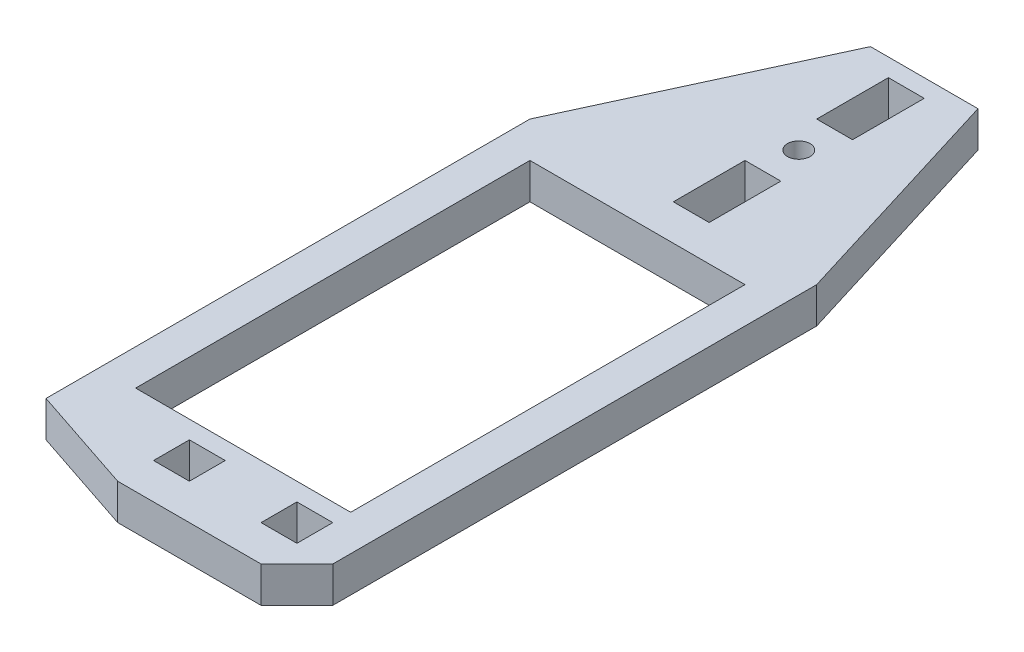
SolidWorks part; units mm, degrees
ref_plane "Front Plane" through (0, 0, 0) normal (0, 0, 1) x (1, 0, 0)
ref_plane "Top Plane" through (0, 0, 0) normal (0, 1, 0) x (1, 0, 0)
ref_plane "Right Plane" through (0, 0, 0) normal (1, 0, 0) x (0, 0, -1)
sketch "Sketch1" plane through (0, 0, 0) normal (0, 1, 0) x (1, 0, 0)
  line L0 (-6.35, 76.2) -> (12.7, 117.475)
  line L1 (0, 0) -> (38.1, 0)
  line L2 (0, 0) -> (0, 69.85)
  line L3 (0, 69.85) -> (38.1, 69.85)
  line L4 (38.1, 0) -> (38.1, 69.85)
  line L5 (-6.35, -15.875) -> (44.45, -15.875)
  line L6 (-6.35, -15.875) -> (-6.35, 76.2)
  line L7 (-6.35, 76.2) -> (44.45, 76.2)
  line L8 (44.45, -15.875) -> (44.45, 76.2)
  line L9 (0, 76.2) -> (38.1, 76.2)
  line L10 (0, 76.2) -> (0, 117.475)
  line L11 (0, 117.475) -> (38.1, 117.475)
  line L12 (38.1, 76.2) -> (38.1, 117.475)
  line L13 (38.1, -3.175) -> (31.75, -3.175)
  line L14 (38.1, -3.175) -> (38.1, -9.525)
  line L15 (38.1, -9.525) -> (31.75, -9.525)
  line L16 (31.75, -3.175) -> (31.75, -9.525)
  line L17 (19.05, -3.175) -> (12.7, -3.175)
  line L18 (19.05, -3.175) -> (19.05, -9.525)
  line L19 (19.05, -9.525) -> (12.7, -9.525)
  line L20 (12.7, -3.175) -> (12.7, -9.525)
  line L21 (19.05, 76.2) -> (25.4, 76.2)
  line L22 (19.05, 76.2) -> (19.05, 88.9)
  line L23 (19.05, 88.9) -> (25.4, 88.9)
  line L24 (25.4, 76.2) -> (25.4, 88.9)
  line L25 (19.05, 101.6) -> (25.4, 101.6)
  line L26 (19.05, 101.6) -> (19.05, 114.3)
  line L27 (19.05, 114.3) -> (25.4, 114.3)
  line L28 (25.4, 101.6) -> (25.4, 114.3)
  line L29 (44.45, 76.2) -> (31.75, 117.475)
  line L30 (12.7, -15.875) -> (-6.35, -9.525)
  line L31 (38.1, -15.875) -> (44.45, -9.525)
  circle A0 centre (22.225, 95.25) radius 2
  dimension "D21" = 4
  dimension "D1" = 38.1
  dimension "D2" = 50.8
  dimension "D3" = 6.35
  dimension "D4" = 15.875
  dimension "D5" = 69.85
  dimension "D6" = 6.35
  dimension "D7" = 41.275
  dimension "D8" = 6.35
  dimension "D9" = 3.175
  dimension "D10" = 6.35
  dimension "D11" = 6.35
  dimension "D12" = 0
  dimension "D13" = 12.7
  dimension "D14" = 12.7
  dimension "D15" = 12.7
  dimension "D16" = 12.7
  dimension "D17" = 12.7
  dimension "D18" = 6.35
  dimension "D19" = 6.35
  dimension "D20" = 0
  dimension "D22" = 6.35
extrude "Boss-Extrude1" add sketch "Sketch1" along normal blind 6.35 contours L12 L29 L11 L0 L10 L7 L22 L23 L24 A0 L28 L25 L26 L27 | L5 L31 L8 L7 L9 L6 L30 L20 L17 L18 L19 L16 L13 L14 L15 L4 L1 L2 L3 | L7 L10 L0 | L7 L29 L12
